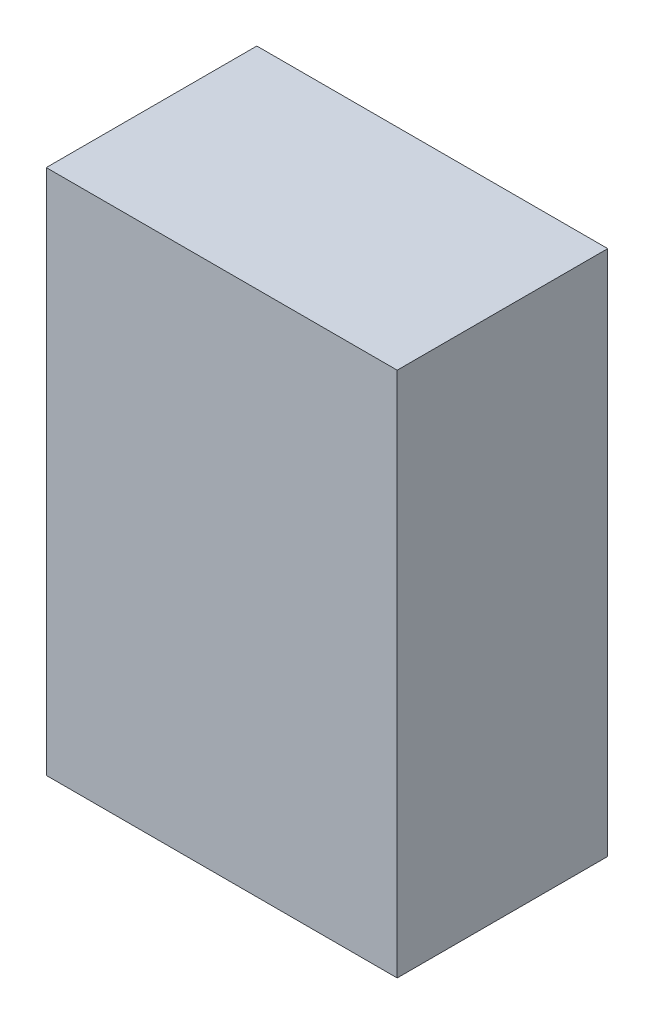
SolidWorks part; units mm, degrees
ref_plane "Front Plane" through (0, 0, 0) normal (0, 0, 1) x (1, 0, 0)
ref_plane "Top Plane" through (0, 0, 0) normal (0, 1, 0) x (1, 0, 0)
ref_plane "Right Plane" through (0, 0, 0) normal (1, 0, 0) x (0, 0, -1)
sketch "Sketch1" plane through (0, 0, 0) normal (0, 1, 0) x (1, 0, 0)
  line L1 (0, 0) -> (50.8, 0)
  line L2 (0, 0) -> (0, 30.48)
  line L3 (0, 30.48) -> (50.8, 30.48)
  line L4 (50.8, 0) -> (50.8, 30.48)
  dimension "D1" = 50.8
  dimension "D2" = 30.48
extrude "Boss-Extrude1" add sketch "Sketch1" along normal blind 76.2
